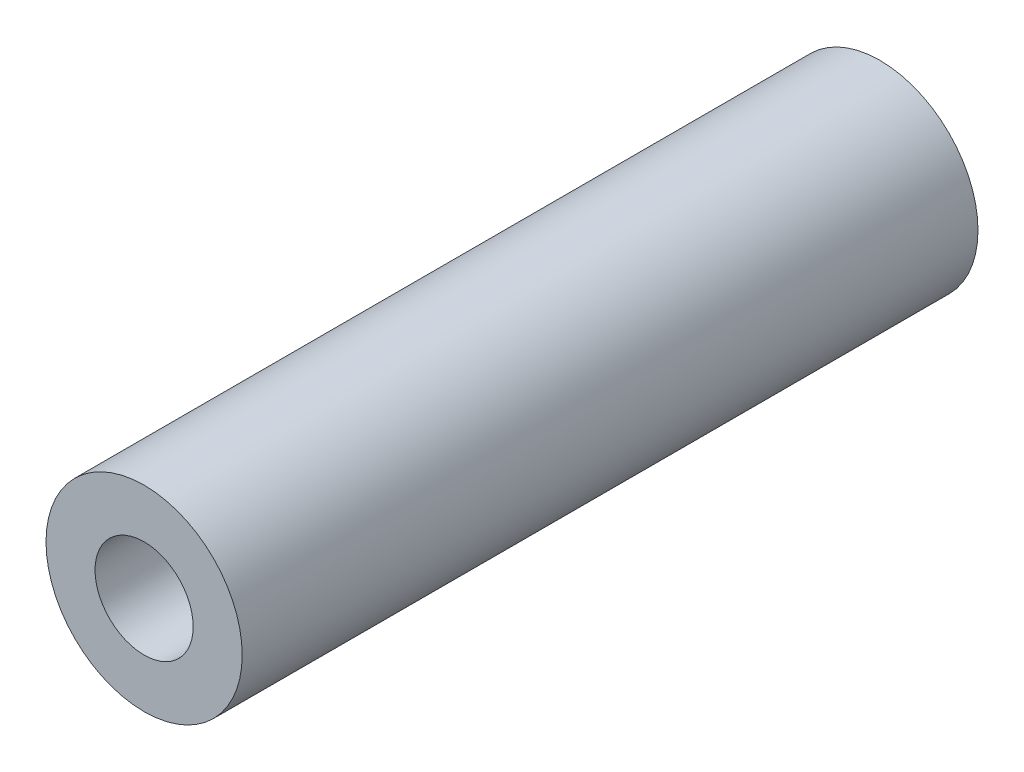
SolidWorks part; units mm, degrees
ref_plane "Front Plane" through (0, 0, 0) normal (0, 0, 1) x (1, 0, 0)
ref_plane "Top Plane" through (0, 0, 0) normal (0, 1, 0) x (1, 0, 0)
ref_plane "Right Plane" through (0, 0, 0) normal (1, 0, 0) x (0, 0, -1)
sketch "Sketch1" plane through (0, 0, 0) normal (0, 0, 1) x (1, 0, 0)
  circle A0 centre (0, 0) radius 4
  dimension "D1" = 8
extrude "Boss-Extrude1" add sketch "Sketch1" along normal blind 30
sketch "Sketch2" plane through (0, 0, 30) normal (0, 0, 1) x (1, 0, 0)
  circle A0 centre (0, 0) radius 2
  dimension "D1" = 4
extrude "Cut-Extrude1" cut sketch "Sketch2" against normal through all
